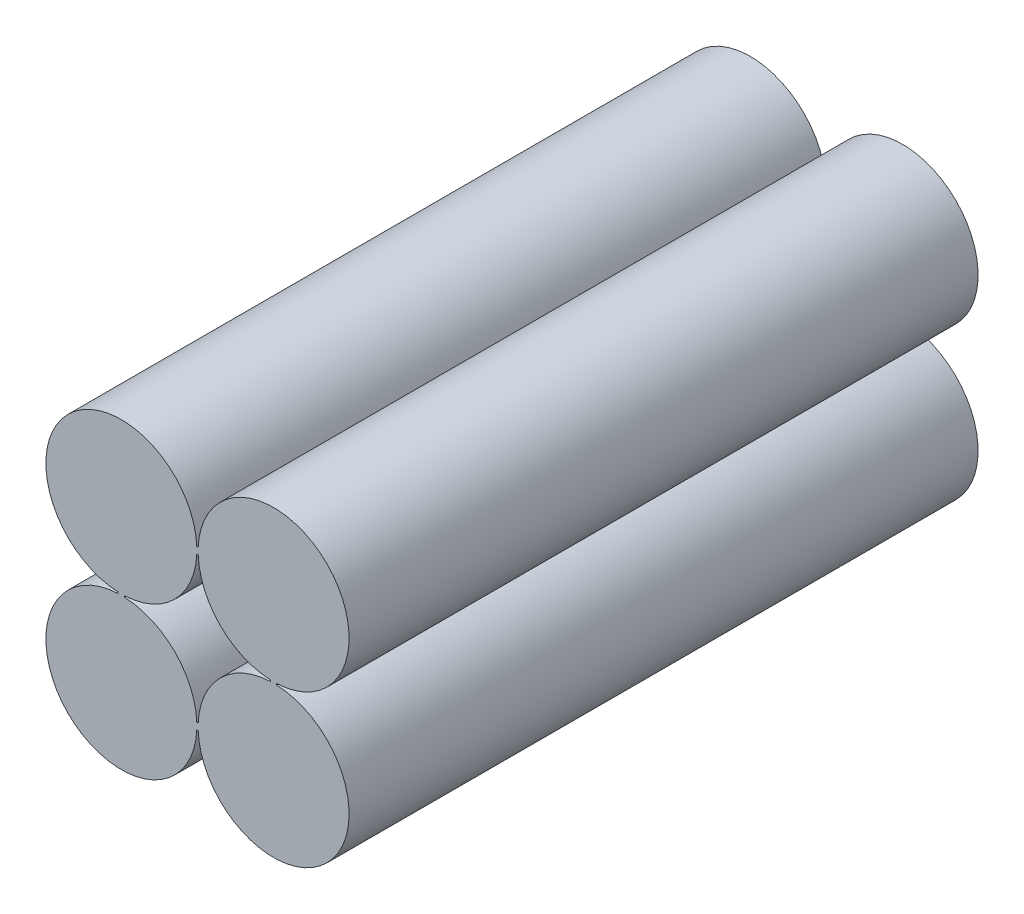
SolidWorks part; units mm, degrees
ref_plane "Front Plane" through (0, 0, 0) normal (0, 0, 1) x (1, 0, 0)
ref_plane "Top Plane" through (0, 0, 0) normal (0, 1, 0) x (1, 0, 0)
ref_plane "Right Plane" through (0, 0, 0) normal (1, 0, 0) x (0, 0, -1)
sketch "Sketch1" plane through (0, 0, 0) normal (0, 0, 1) x (1, 0, 0)
  line L0 (4.6047, -6.05) -> (7.7782, -6.05) construction
  line L1 (5.9948, 0.25) -> (6.1052, 0.25)
  line L3 (5.9948, -0.25) -> (6.1052, -0.25)
  line L5 (6.05, -3.1671) -> (6.05, -8.2034) construction
  line L6 (5.9948, -11.85) -> (6.1052, -11.85)
  line L8 (5.9948, -12.35) -> (6.1052, -12.35)
  line L12 (-0.25, -5.9948) -> (-0.25, -6.1052)
  line L14 (0.25, -5.9948) -> (0.25, -6.1052)
  line L15 (11.85, -5.9948) -> (11.85, -6.1052)
  line L17 (12.35, -5.9948) -> (12.35, -6.1052)
  arc A0 (0.25, -5.9948) -> (5.9948, -0.25) centre (0, 0) ccw
  arc A1 (12.35, -5.9948) -> (6.1052, 0.25) centre (12.1, 0) ccw
  arc A2 (11.85, -6.1052) -> (6.1052, -11.85) centre (12.1, -12.1) ccw
  arc A3 (-0.25, -6.1052) -> (5.9948, -12.35) centre (0, -12.1) ccw
  arc A4 (6.1052, -0.25) -> (11.85, -5.9948) centre (12.1, 0) ccw
  arc A5 (5.9948, 0.25) -> (-0.25, -5.9948) centre (0, 0) ccw
  arc A6 (6.1052, -12.35) -> (12.35, -6.1052) centre (12.1, -12.1) ccw
  arc A7 (5.9948, -11.85) -> (0.25, -6.1052) centre (0, -12.1) ccw
  dimension "D1" = 12
  dimension "D2" = 12
  dimension "D3" = 12
  dimension "D4" = 12
  dimension "D5" = 12.1
  dimension "D6" = 12.1
  dimension "D7" = 12.1
  dimension "D9" = 0.25
  dimension "D10" = 6.05
  dimension "D11" = 6.05
  dimension "D15" = 0.25
extrude "Boss-Extrude1" add sketch "Sketch1" along normal blind 50
